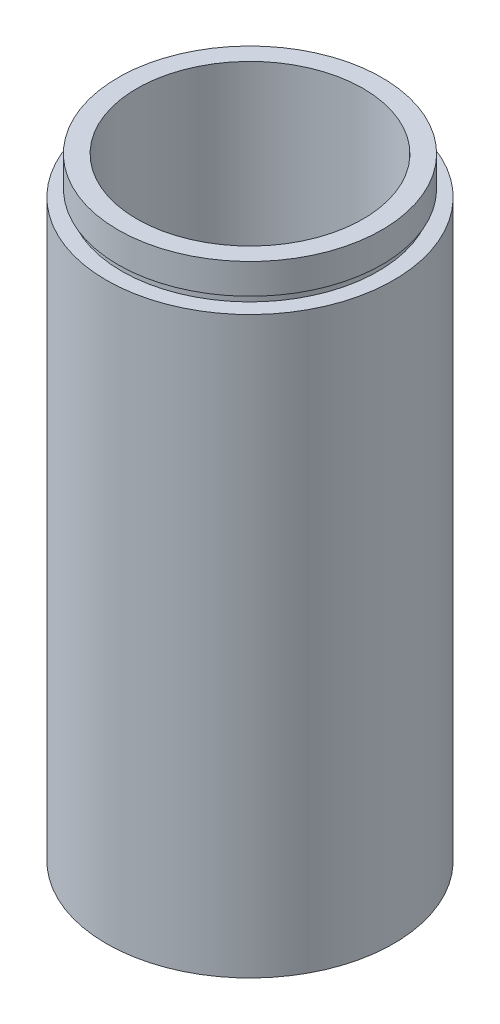
SolidWorks part; units mm, degrees
ref_plane "前视基准面" through (0, 0, 0) normal (0, 0, 1) x (1, 0, 0)
ref_plane "上视基准面" through (0, 0, 0) normal (0, 1, 0) x (1, 0, 0)
ref_plane "右视基准面" through (0, 0, 0) normal (1, 0, 0) x (0, 0, -1)
sketch "草图1" plane through (0, 0, 0) normal (0, 0, 1) x (1, 0, 0)
  line L0 (0, 161.3762) -> (0, 0) construction
  line L1 (141.7365, 0) -> (-131.7984, 0) construction
  line L2 (19.05, 0) -> (19.05, 76.2)
  line L3 (17, 4.5) -> (17.6, 4.5)
  line L4 (17, 0) -> (19.05, 0)
  line L5 (17.6, 4.5) -> (17.6, 5.5)
  line L6 (15, 5.5) -> (15, 81.2)
  line L7 (17, 4.5) -> (17, 0)
  line L8 (17.6, 5.5) -> (15, 5.5)
  line L9 (17, 77.2) -> (17, 76.2)
  line L10 (19.05, 76.2) -> (17, 76.2)
  line L11 (17.5, 77.2) -> (17.5, 81.2)
  line L12 (17, 77.2) -> (17.5, 77.2)
  line L13 (17.5, 81.2) -> (15, 81.2)
  dimension "D2" = 19.05
  dimension "D3" = 17.6
  dimension "D4" = 15
  dimension "D5" = 17
  dimension "D6" = 17.5
  dimension "D7" = 1
  dimension "D8" = 76.2
  dimension "D9" = 5
  dimension "D10" = 1
  dimension "D11" = 17
revolve "旋转1" add sketch "草图1" angle 360 about L0
cosmetic thread "装饰螺纹线1"
cosmetic thread "装饰螺纹线2"
cosmetic thread "装饰螺纹线3"
